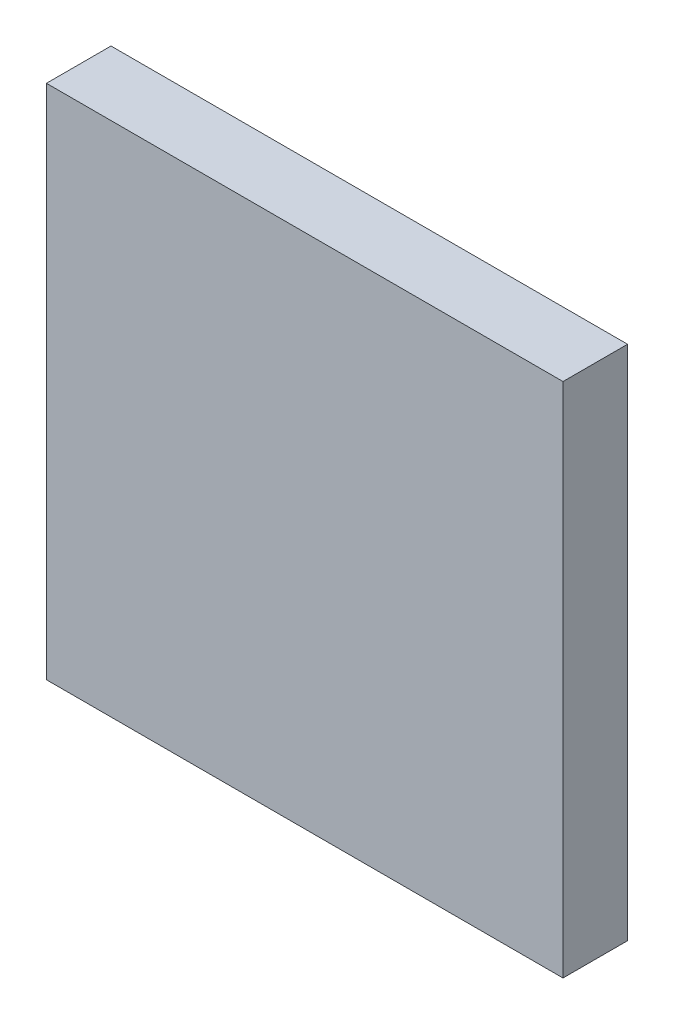
SolidWorks part; units mm, degrees
ref_plane "Front Plane" through (0, 0, 0) normal (0, 0, 1) x (1, 0, 0)
ref_plane "Top Plane" through (0, 0, 0) normal (0, 1, 0) x (1, 0, 0)
ref_plane "Right Plane" through (0, 0, 0) normal (1, 0, 0) x (0, 0, -1)
sketch "Sketch1" plane through (0, 0, 0) normal (0, 0, 1) x (1, 0, 0)
  line L1 (-40, 40) -> (40, 40)
  line L2 (-40, 40) -> (-40, -40)
  line L3 (-40, -40) -> (40, -40)
  line L4 (40, 40) -> (40, -40)
  point P5 (0, 40)
  point P7 (40, 0)
  dimension "D1" = 80
extrude "Boss-Extrude1" add sketch "Sketch1" along normal blind 10 contours L1 L4 L3 L2
